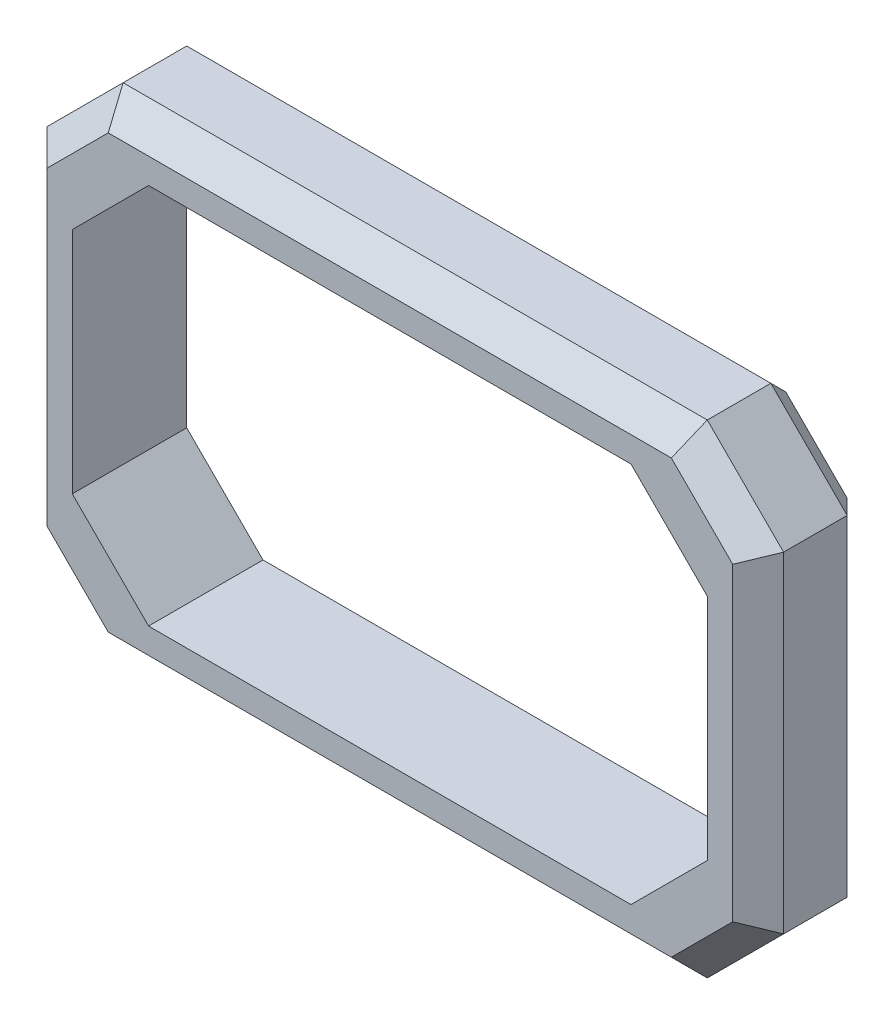
SolidWorks part; units mm, degrees
ref_plane "Plano frontal" through (0, 0, 0) normal (0, 0, 1) x (1, 0, 0)
ref_plane "Plano superior" through (0, 0, 0) normal (0, 1, 0) x (1, 0, 0)
ref_plane "Plano direito" through (0, 0, 0) normal (1, 0, 0) x (0, 0, -1)
sketch "Esboço1" plane through (0, 0, 0) normal (0, 0, 1) x (1, 0, 0)
  line L1 (-124.8381, -75) -> (124.8381, -75)
  line L2 (-124.8381, -75) -> (-124.8381, 75)
  line L3 (-124.8381, 75) -> (124.8381, 75)
  line L4 (124.8381, -75) -> (124.8381, 75)
  line L5 (-124.8381, -75) -> (124.8381, 75) construction
  line L6 (-124.8381, 75) -> (124.8381, -75) construction
  line L7 (144.8381, -95) -> (-144.8381, -95)
  line L8 (144.8381, -95) -> (144.8381, 95)
  line L9 (144.8381, 95) -> (-144.8381, 95)
  line L10 (-144.8381, -95) -> (-144.8381, 95)
  line L11 (144.8381, -95) -> (-144.8381, 95) construction
  line L12 (144.8381, 95) -> (-144.8381, -95) construction
  point P0 (0, 0)
  point P5 (0, 0)
  dimension "D1" = 20
  dimension "D2" = 20
extrude "Ressalto-extrusão1" add sketch "Esboço1" along normal blind 45
chamfer "Chanfro1" distance 30 angle 45 8 edges at (-124.8381, -75, 22.5) (124.8381, -75, 22.5) (124.8381, 75, 22.5) (-124.8381, 75, 22.5) (144.8381, -95, 22.5) (144.8381, 95, 22.5) (-144.8381, -95, 22.5) (-144.8381, 95, 22.5)
chamfer "Chanfro2" distance 10 angle 45 16 edges at (-129.8381, -80, 45) (-144.8381, 0, 45) (-129.8381, 80, 45) (0, 95, 45) (129.8381, 80, 45) (144.8381, 0, 45) (129.8381, -80, 45) (0, -95, 45) (129.8381, 80, 0) (0, 95, 0) (-129.8381, 80, 0) (-144.8381, 0, 0) (-129.8381, -80, 0) (0, -95, 0) (129.8381, -80, 0) (144.8381, 0, 0)
